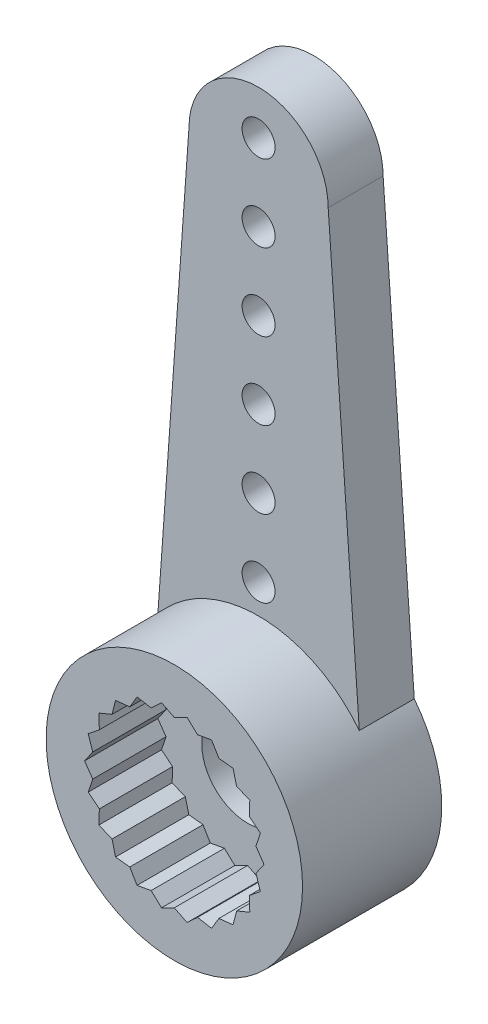
SolidWorks part; units mm, degrees
ref_plane "Front Plane" through (0, 0, 0) normal (0, 0, 1) x (1, 0, 0)
ref_plane "Top Plane" through (0, 0, 0) normal (0, 1, 0) x (1, 0, 0)
ref_plane "Right Plane" through (0, 0, 0) normal (1, 0, 0) x (0, 0, -1)
sketch "Sketch1" plane through (0, 0, 0) normal (0, 1, 0) x (1, 0, 0)
  line L0 (3.5, 0) -> (0, 0)
  line L1 (0, 0) -> (0, -3.8)
  line L2 (0, -3.8) -> (3.5, -3.8)
  line L3 (3.5, -3.8) -> (3.5, 0)
  line L4 (0, 0) -> (0, -3.8) construction
revolve "Revolve1" add sketch "Sketch1" angle 360 about L4
ref_plane "Plane1" through (0, 0, 0) normal (0, 0, -1) x (-1, 0, 0)
sketch "Sketch2" plane through (0, 0, 0) normal (0, 0, -1) x (-1, 0, 0)
  line L0 (-1.9, 14.1) -> (-2.75, 2.1651)
  line L1 (2.75, 2.1651) -> (1.9, 14.1)
  arc A0 (1.9, 14.1) -> (-1.9, 14.1) centre (0, 14.1) ccw
  arc A1 (-2.75, 2.1651) -> (2.75, 2.1651) centre (0, 0) cw
extrude "Boss-Extrude1" add sketch "Sketch2" against normal blind 1.5
sketch "Sketch3" plane through (0, 0, 3.8) normal (0, 0, 1) x (1, 0, 0)
  line L0 (2.0603, 1.3241) -> (1.7004, 1.4734)
  line L1 (1.7004, 1.4734) -> (1.6038, 1.8509)
  line L2 (1.6038, 1.8509) -> (1.2164, 1.8928)
  line L3 (1.2164, 1.8928) -> (1.0174, 2.2278)
  line L4 (1.0174, 2.2278) -> (0.6339, 2.1589)
  line L5 (0.6339, 2.1589) -> (0.3485, 2.4241)
  line L6 (0.3485, 2.4241) -> (0, 2.25)
  line L7 (0, 2.25) -> (-0.3485, 2.4241)
  line L8 (-0.3485, 2.4241) -> (-0.6339, 2.1589)
  line L9 (-0.6339, 2.1589) -> (-1.0174, 2.2278)
  line L10 (-1.0174, 2.2278) -> (-1.2164, 1.8928)
  line L11 (-1.2164, 1.8928) -> (-1.6038, 1.8509)
  line L12 (-1.6038, 1.8509) -> (-1.7004, 1.4734)
  line L13 (-1.7004, 1.4734) -> (-2.0603, 1.3241)
  line L14 (-2.0603, 1.3241) -> (-2.0467, 0.9347)
  line L15 (-2.0467, 0.9347) -> (-2.3499, 0.69)
  line L16 (-2.3499, 0.69) -> (-2.2271, 0.3202)
  line L17 (-2.2271, 0.3202) -> (-2.4491, 0)
  line L18 (-2.4491, 0) -> (-2.2271, -0.3202)
  line L19 (-2.2271, -0.3202) -> (-2.3499, -0.69)
  line L20 (-2.3499, -0.69) -> (-2.0467, -0.9347)
  line L21 (-2.0467, -0.9347) -> (-2.0603, -1.3241)
  line L22 (-2.0603, -1.3241) -> (-1.7004, -1.4734)
  line L23 (-1.7004, -1.4734) -> (-1.6038, -1.8509)
  line L24 (-1.6038, -1.8509) -> (-1.2164, -1.8928)
  line L25 (-1.2164, -1.8928) -> (-1.0174, -2.2278)
  line L26 (-1.0174, -2.2278) -> (-0.6339, -2.1589)
  line L27 (-0.6339, -2.1589) -> (-0.3485, -2.4241)
  line L28 (-0.3485, -2.4241) -> (0, -2.25)
  line L29 (0, -2.25) -> (0.3485, -2.4241)
  line L30 (0.3485, -2.4241) -> (0.6339, -2.1589)
  line L31 (0.6339, -2.1589) -> (1.0174, -2.2278)
  line L32 (1.0174, -2.2278) -> (1.2164, -1.8928)
  line L33 (1.2164, -1.8928) -> (1.6038, -1.8509)
  line L34 (1.6038, -1.8509) -> (1.7004, -1.4734)
  line L35 (1.7004, -1.4734) -> (2.0603, -1.3241)
  line L36 (2.0603, -1.3241) -> (2.0467, -0.9347)
  line L37 (2.0467, -0.9347) -> (2.3499, -0.69)
  line L38 (2.3499, -0.69) -> (2.2271, -0.3202)
  line L39 (2.2271, -0.3202) -> (2.4491, 0)
  line L40 (2.4491, 0) -> (2.2271, 0.3202)
  line L41 (2.2271, 0.3202) -> (2.3499, 0.69)
  line L42 (2.3499, 0.69) -> (2.0467, 0.9347)
  line L43 (2.0467, 0.9347) -> (2.0603, 1.3241)
extrude "Cut-Extrude1" cut sketch "Sketch3" against normal blind 2
hole_wizard "Ø0.9 (0.9) Diameter Hole1" positions "Sketch5" profile "Sketch4" hole size "Ø0.9" standard "ANSI Metric"
sketch "Sketch5" plane through (0, 0, 0) normal (0, 0, -1) x (-1, 0, 0)
  point P0 (0, 10.6)
  point P1 (0, 12.7)
  point P2 (0, 14.8)
  point P3 (0, 6.4)
  point P4 (0, 8.5)
  point P5 (0, 4.3)
sketch "Sketch4" plane through (0, 10.6, 0) normal (1, 0, 0) x (0, 1, 0)
  line L0 (0, 0) -> (0, 3.8)
  line L1 (0, 3.8) -> (0.45, 3.8)
  line L2 (0.45, 3.8) -> (0.45, 0)
  line L5 (0.45, 0) -> (0, 0)
  line L11 (0, -6.35) -> (0, 107.95) construction
  dimension "Thru Hole Dia." = 0.9
  dimension "Thru Hole Depth" = 3.8
hole_wizard "CBORE for M2 Hex Head Machine Screw1" positions "Sketch7" profile "Sketch6" counterbore size "M2" standard "ANSI Metric"
sketch "Sketch7" plane through (0, 0, 0) normal (0, 0, -1) x (-1, 0, 0)
  point P0 (0, 0)
sketch "Sketch6" plane through (0, 0, 0) normal (1, 0, 0) x (0, 1, 0)
  line L0 (0, 0) -> (0, 3.8)
  line L1 (0, 3.8) -> (1.25, 3.8)
  line L3 (1.25, 3.8) -> (1.25, 1)
  line L4 (1.25, 1) -> (2.35, 1)
  line L5 (2.35, 1) -> (2.35, 0)
  line L7 (2.35, 0) -> (0, 0)
  line L11 (0, -6.35) -> (0, 107.95) construction
  dimension "Thru Hole Dia." = 2.5
  dimension "Thru Hole Depth" = 3.8
  dimension "C'Bore Dia." = 4.7
  dimension "C'Bore Depth" = 1
